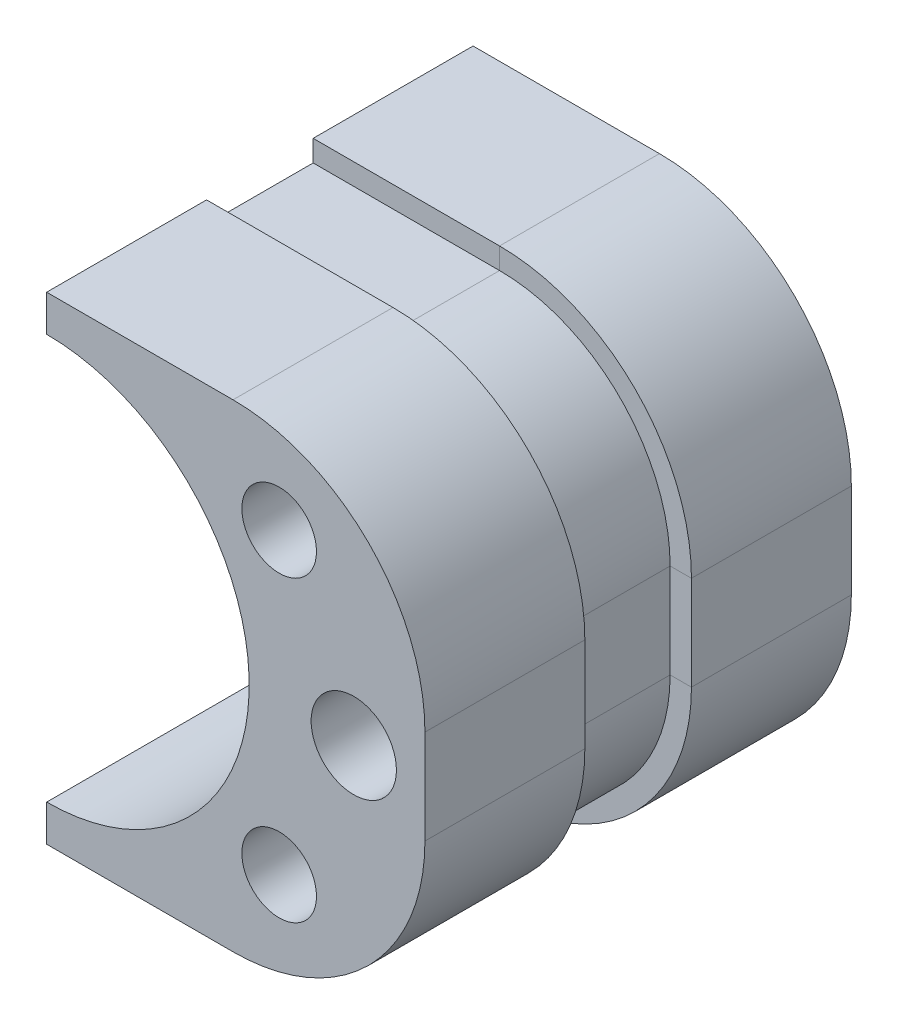
SolidWorks part; units mm, degrees
material "ABS"
ref_plane "Plano frontal" through (0, 0, 0) normal (0, 0, 1) x (1, 0, 0)
ref_plane "Plano superior" through (0, 0, 0) normal (0, 1, 0) x (1, 0, 0)
ref_plane "Plano direito" through (0, 0, 0) normal (1, 0, 0) x (0, 0, -1)
sketch "Esboço1" plane through (0, 0, 0) normal (0, 0, 1) x (1, 0, 0)
  line L0 (0.1126, 0) -> (53.4799, 0) construction
  line L2 (0.1126, -22.4239) -> (0.1126, -19)
  line L6 (0.1126, 19) -> (0.1126, 22.4239)
  line L7 (0.1126, 22.4239) -> (17.5982, 22.4239)
  line L8 (35.5982, 4.4239) -> (35.5982, -4.4239)
  line L9 (0.1126, -22.4239) -> (17.5982, -22.4239)
  arc A0 (0.1126, -19) -> (0.1126, 19) centre (0.1126, 0) ccw
  circle A1 centre (21.9232, -14) radius 1.3931
  circle A3 centre (21.9232, 14) radius 1.3931
  circle A4 centre (28.9232, 0) radius 4
  arc A5 (17.5982, 22.4239) -> (35.5982, 4.4239) centre (17.5982, 4.4239) cw
  arc A6 (35.5982, -4.4239) -> (17.5982, -22.4239) centre (17.5982, -4.4239) cw
  point P1 (0.1126, 0)
  dimension "D3" = 19
  dimension "D6" = 17.4856
  dimension "D4" = 28.8106
  dimension "D5" = 18
  dimension "D1" = 7
  dimension "D2" = 14
extrude "Ressalto-extrusão1" add sketch "Esboço1" along normal blind 40 contours A0 L0 A4 L8 A5 L7 L6 A3 | L0 A0 L2 L9 A6 L8 A4 A1
sketch "Esboço8" plane through (0.1126, 0, 0) normal (-1, 0, 0) x (0, 0, 1)
  line L0 (40, 22.4239) -> (0, 22.4239) construction
  line L5 (15, 22.4239) -> (25, 22.4239)
  line L6 (15, 22.4239) -> (15, 20.4239)
  line L7 (15, 20.4239) -> (25, 20.4239)
  line L8 (25, 22.4239) -> (25, 20.4239)
  point P0 (20, 22.4239)
  point P1 (20, 22.4239)
  dimension "D3" = 2
  dimension "D4" = 10
sketch "Esboço9" plane through (0, 0, 40) normal (0, 0, 1) x (1, 0, 0)
  line L10 (0.1126, -19) -> (0.1126, -22.4239)
  line L11 (0.1126, -22.4239) -> (17.5982, -22.4239)
  line L12 (35.5982, -4.4239) -> (35.5982, 4.4239)
  line L13 (17.5982, 22.4239) -> (0.1126, 22.4239)
  line L14 (0.1126, 22.4239) -> (0.1126, 19)
  line L16 (0.1126, -22.4239) -> (17.5982, -22.4239)
  line L17 (35.5982, -4.4239) -> (35.5982, 4.4239)
  line L18 (17.5982, 22.4239) -> (0.1126, 22.4239)
  arc A6 (0.1126, -19) -> (0.1126, 19) centre (0.1126, 0) ccw
  arc A7 (17.5982, -22.4239) -> (35.5982, -4.4239) centre (17.5982, -4.4239) ccw
  arc A8 (35.5982, 4.4239) -> (17.5982, 22.4239) centre (17.5982, 4.4239) ccw
  arc A10 (17.5982, -22.4239) -> (35.5982, -4.4239) centre (17.5982, -4.4239) ccw
  arc A11 (35.5982, 4.4239) -> (17.5982, 22.4239) centre (17.5982, 4.4239) ccw
  dimension "D1" = 0
sweep "Varredura de corte1" cut profiles "Esboço8" path "Esboço9"
sketch "Esboço10" plane through (0, 0, 40) normal (0, 0, 1) x (1, 0, 0)
  circle A1 centre (21.9232, 14) radius 3.5
  circle A2 centre (21.9232, -14) radius 3.5
  dimension "D1" = 7
extrude "Corte-extrusão1" cut sketch "Esboço10" against normal blind 10
